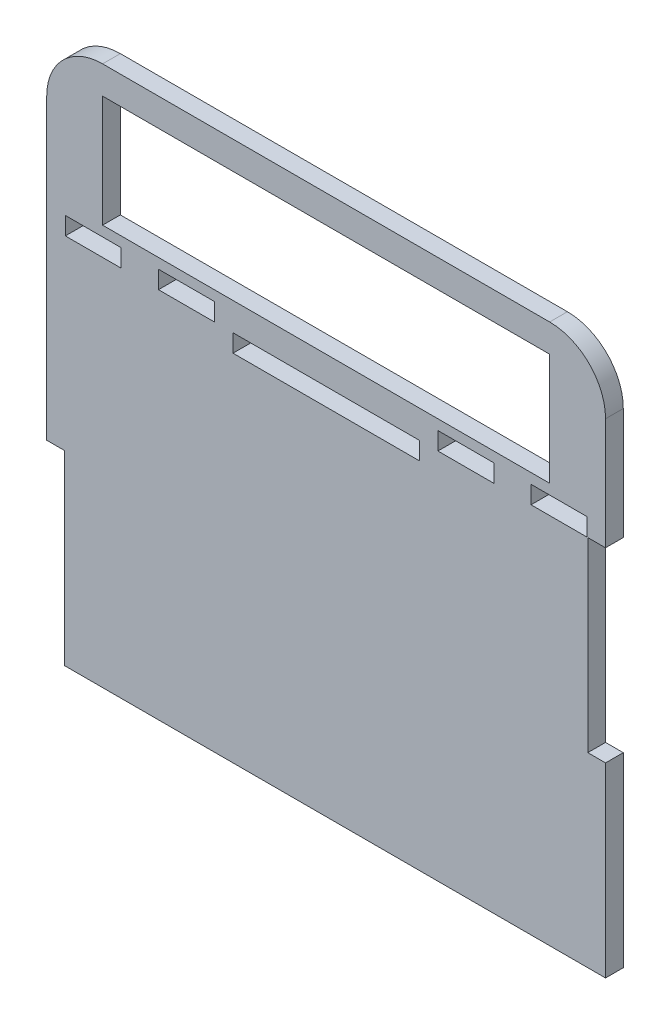
SolidWorks part; units mm, degrees
ref_plane "Front Plane" through (0, 0, 0) normal (0, 0, 1) x (1, 0, 0)
ref_plane "Top Plane" through (0, 0, 0) normal (0, 1, 0) x (1, 0, 0)
ref_plane "Right Plane" through (0, 0, 0) normal (1, 0, 0) x (0, 0, -1)
sketch "Sketch1" plane through (0, 0, 0) normal (0, 0, 1) x (1, 0, 0)
  line L0 (-50, 16.6667) -> (-50, 50)
  line L1 (46.825, -50) -> (-50, -50) construction
  line L2 (50, -16.6667) -> (50, 16.6667)
  line L4 (-50, -50) -> (-50, -16.6667) construction
  line L5 (50, -50) -> (-50, 50) construction
  line L6 (50, 50) -> (-50, -50) construction
  line L11 (-50, 16.6667) -> (-46.825, 16.6667)
  line L13 (-50, -16.6667) -> (-46.825, -16.6667) construction
  line L14 (-46.825, 16.6667) -> (-46.825, -16.6667)
  line L15 (50, 16.6667) -> (46.825, 16.6667)
  line L18 (46.825, 16.6667) -> (46.825, 50)
  line L21 (50, -16.6667) -> (46.825, -16.6667)
  line L22 (46.825, -50) -> (46.825, -16.6667) construction
  line L25 (46.825, 50) -> (50, 50)
  line L27 (-16.6667, 50) -> (-16.6667, 46.825)
  line L28 (-16.6667, 46.825) -> (16.6667, 46.825)
  line L29 (16.6667, 50) -> (16.6667, 46.825)
  line L34 (-16.6667, 50) -> (16.6667, 50)
  line L35 (-50, 50) -> (-50, 80)
  line L36 (-50, 80) -> (50, 80)
  line L37 (50, 50) -> (50, 80)
  line L38 (-16.6667, 50) -> (16.6667, 50)
  line L39 (40, 55) -> (-40, 55)
  line L40 (40, 55) -> (40, 75)
  line L41 (40, 75) -> (-40, 75)
  line L42 (-40, 55) -> (-40, 75)
  line L43 (-46.825, -16.6667) -> (46.825, -16.6667)
  point P0 (0, 0)
  dimension "D1" = 100
  dimension "D2" = 100
  dimension "D4" = 33.3333
  dimension "D5" = 33.3333
  dimension "D6" = 33.3333
  dimension "D7" = 33.3333
  dimension "D8" = 33.3333
  dimension "D10" = 3.175
  dimension "D11" = 3.175
  dimension "D9" = 3.175
  dimension "D3" = 33.3333
  dimension "D12" = 3.175
  dimension "D13" = 30
  dimension "D14" = 100
  dimension "D15" = 20
  dimension "D16" = 80
  dimension "D17" = 10
  dimension "D18" = 5
extrude "Boss-Extrude1" add sketch "Sketch1" along normal blind 3.175 contours L25 L37 L36 L35 L0 L11 L14 L13 L4 L1 L22 L21 L2 L15 L18 L27 L34 L29 L28 L39 L42 L41 L40
fillet "Fillet1" radius 10 2 edges at (50, 80, 1.5875) (-50, 80, 1.5875)
sketch "Sketch2" plane through (0, 0, 3.175) normal (0, 0, 1) x (1, 0, 0)
  line L0 (-16.6667, 50) -> (-50, 50) construction
  line L1 (-50, 16.6667) -> (-50, 70) construction
  line L2 (0, 50) -> (0, 46.825) construction
  line L3 (-16.6667, 50) -> (16.6667, 50) construction
  line L4 (-16.6667, 46.825) -> (16.6667, 46.825) construction
  line L5 (30, 53.175) -> (20, 53.175)
  line L6 (-46.6667, 50) -> (-36.6667, 50)
  line L7 (-46.6667, 50) -> (-46.6667, 53.175)
  line L8 (-46.6667, 53.175) -> (-36.6667, 53.175)
  line L9 (-36.6667, 50) -> (-36.6667, 53.175)
  line L10 (-30, 50) -> (-20, 50)
  line L11 (-30, 50) -> (-30, 53.175)
  line L12 (-30, 53.175) -> (-20, 53.175)
  line L13 (-20, 50) -> (-20, 53.175)
  line L14 (20, 50) -> (20, 53.175)
  line L15 (30, 50) -> (20, 50)
  line L16 (30, 50) -> (30, 53.175)
  line L17 (46.6667, 53.175) -> (36.6667, 53.175)
  line L18 (36.6667, 50) -> (36.6667, 53.175)
  line L19 (46.6667, 50) -> (36.6667, 50)
  line L20 (46.6667, 50) -> (46.6667, 53.175)
  dimension "D1" = 10
  dimension "D2" = 3.175
  dimension "D3" = 3.3333
  dimension "D4" = 6.6667
  dimension "D5" = 10
  dimension "D6" = 3.175
extrude "Cut-Extrude1" cut sketch "Sketch2" against normal blind 3.175
equation "\"BoxLength\"=10"
equation "\"D1@Sketch1\"=\"BoxLength\""
equation "\"D2@Sketch1\"=\"BoxLength\""
